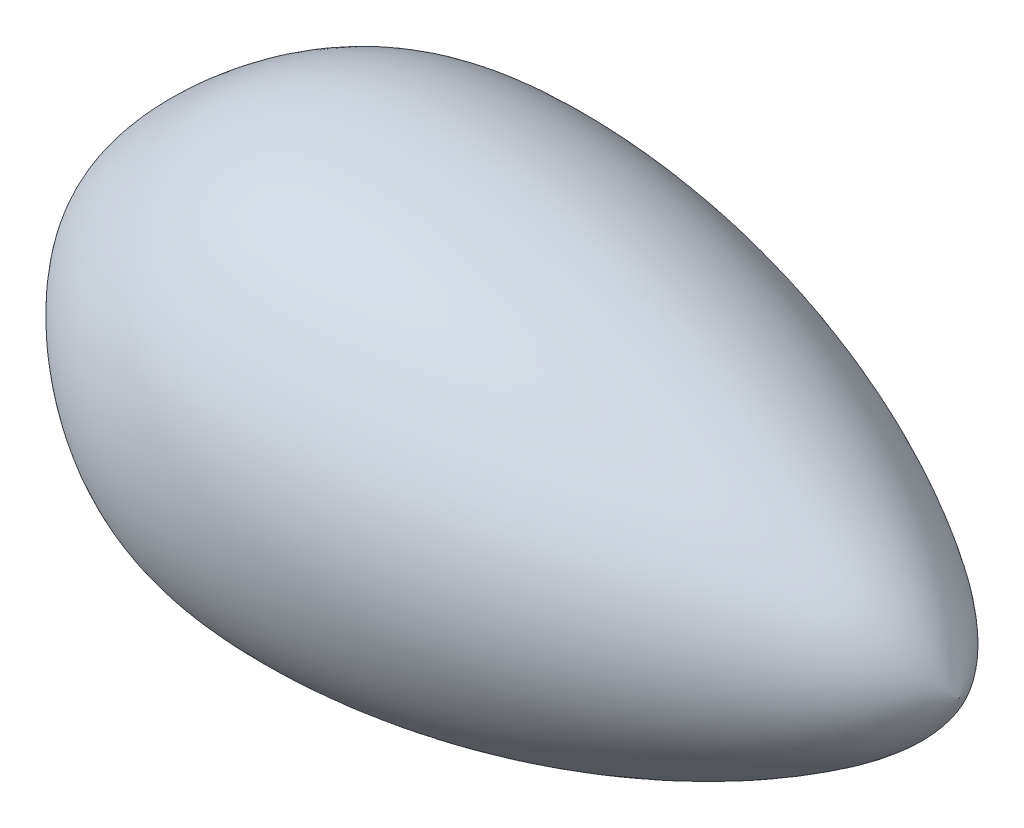
SolidWorks part; units mm, degrees
ref_plane "Plan de face" through (0, 0, 0) normal (0, 0, 1) x (1, 0, 0)
ref_plane "Plan de dessus" through (0, 0, 0) normal (0, 1, 0) x (1, 0, 0)
ref_plane "Plan de droite" through (0, 0, 0) normal (1, 0, 0) x (0, 0, -1)
sketch "Esquisse1" plane through (0, 0, 0) normal (0, 1, 0) x (1, 0, 0)
  line L0 (-269.6158, 0) -> (2459.3297, 0) construction
  line L4 (0, 0) -> (2370, 0)
  line L5 (41.8657, 625) -> (2257.8035, 625) construction
  spline S1 degree 3 poles (0, 0) (4.7042, 30.0006) (3.1278, 179.1227) (368.5183, 571.4409) (1076.4168, 685.9033) (1909.8579, 454.4287) (2319.8709, 127.3308) (2370, 0) knots 0 0 0 0 0.042417 0.222214 0.402801 0.855939 1 1 1 1
  dimension "D1" = 2370
  dimension "D2" = 625
revolve "Révolution1" add sketch "Esquisse1" angle 360 about L0
